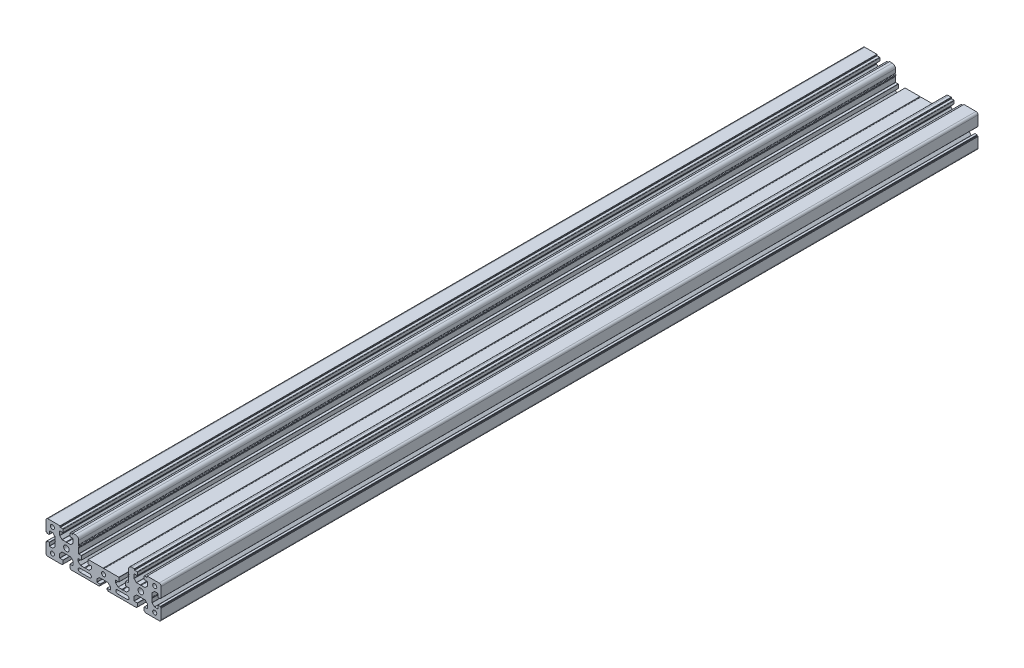
SolidWorks part; units mm, degrees
material "6063-T6"
ref_plane "Спереди" through (0, 0, 0) normal (0, 0, 1) x (1, 0, 0)
ref_plane "Сверху" through (0, 0, 0) normal (0, 1, 0) x (1, 0, 0)
ref_plane "Справа" through (0, 0, 0) normal (1, 0, 0) x (0, 0, -1)
sketch "Эскиз1" plane through (0, 0, 0) normal (0, 0, 1) x (1, 0, 0)
  line L2 (29, -16.95) -> (17, -16.95)
  line L3 (17, -12.75) -> (29, -12.75)
  line L4 (-29, -12.75) -> (-17, -12.75)
  line L5 (-17, -16.95) -> (-29, -16.95)
  line L6 (-53.1, 18.7) -> (-53.1, 19.8)
  line L7 (-53.3, 20) -> (-68, 20)
  line L8 (-70.5, 17.5) -> (-70.5, 5.4)
  line L9 (-70.3, 5.2) -> (-69.7, 5.2)
  line L10 (-69.5, 5) -> (-69.5, 4.3)
  line L11 (-69.3, 4.1) -> (-66.7, 4.1)
  line L12 (-66.5, 4.3) -> (-66.5, 8.05)
  line L13 (-66.3, 8.25) -> (-62.3828, 8.25)
  line L14 (-62.2414, 8.1914) -> (-59.3586, 5.3086)
  line L15 (-59.3, 5.1672) -> (-59.3, 0.6245)
  line L16 (-59.3, -0.6245) -> (-59.3, -5.1672)
  line L17 (-59.3586, -5.3086) -> (-62.2414, -8.1914)
  line L18 (-62.3828, -8.25) -> (-66.3, -8.25)
  line L19 (-66.5, -8.05) -> (-66.5, -4.3)
  line L20 (-66.7, -4.1) -> (-69.3, -4.1)
  line L21 (-69.5, -4.3) -> (-69.5, -5)
  line L22 (-69.7, -5.2) -> (-70.3, -5.2)
  line L23 (-70.5, -5.4) -> (-70.5, -17.5)
  line L24 (-68, -20) -> (-50.8, -20)
  line L25 (-50.6, -19.8) -> (-50.6, -19.2)
  line L26 (-50.4, -19) -> (-49.8, -19)
  line L27 (-49.6, -18.8) -> (-49.6, -14.7)
  line L28 (-49.8, -14.5) -> (-53.55, -14.5)
  line L29 (-53.75, -14.3) -> (-53.75, -9.7071)
  line L30 (-53.6036, -9.3536) -> (-50.8964, -6.6464)
  line L31 (-50.5429, -6.5) -> (-46.1245, -6.5)
  line L32 (-44.8755, -6.5) -> (-40.4571, -6.5)
  line L33 (-40.1036, -6.6464) -> (-37.3964, -9.3536)
  line L34 (-37.25, -9.7071) -> (-37.25, -14.3)
  line L35 (-37.45, -14.5) -> (-41.2, -14.5)
  line L36 (-41.4, -14.7) -> (-41.4, -18.8)
  line L37 (-41.2, -19) -> (-40.6, -19)
  line L38 (-40.4, -19.2) -> (-40.4, -19.8)
  line L39 (-40.2, -20) -> (-23.6245, -20)
  line L40 (-22.3755, -20) -> (-5.4, -20)
  line L41 (-5.2, -19.8) -> (-5.2, -19.2)
  line L42 (-5, -19) -> (-4.3, -19)
  line L43 (-4.1, -18.8) -> (-4.1, -17.5)
  line L44 (-4.3, -17.3) -> (-8.05, -17.3)
  line L45 (-8.25, -17.1) -> (-8.25, -13.8828)
  line L46 (-8.1914, -13.7414) -> (-5.3086, -10.8586)
  line L47 (-5.1672, -10.8) -> (-0.6245, -10.8)
  line L48 (0.6245, -10.8) -> (5.1672, -10.8)
  line L49 (5.3086, -10.8586) -> (8.1914, -13.7414)
  line L50 (8.25, -13.8828) -> (8.25, -17.1)
  line L51 (8.05, -17.3) -> (4.3, -17.3)
  line L52 (4.1, -17.5) -> (4.1, -18.8)
  line L53 (4.3, -19) -> (5, -19)
  line L54 (5.2, -19.2) -> (5.2, -19.8)
  line L55 (5.4, -20) -> (22.3755, -20)
  line L56 (23.6245, -20) -> (40.2, -20)
  line L57 (40.4, -19.8) -> (40.4, -19.2)
  line L58 (40.6, -19) -> (41.2, -19)
  line L59 (41.4, -18.8) -> (41.4, -14.7)
  line L60 (41.2, -14.5) -> (37.45, -14.5)
  line L61 (37.25, -14.3) -> (37.25, -9.7071)
  line L62 (37.3964, -9.3536) -> (40.1036, -6.6464)
  line L63 (40.4571, -6.5) -> (44.8755, -6.5)
  line L64 (46.1245, -6.5) -> (50.5429, -6.5)
  line L65 (50.8964, -6.6464) -> (53.6036, -9.3536)
  line L66 (53.75, -9.7071) -> (53.75, -14.3)
  line L67 (53.55, -14.5) -> (49.8, -14.5)
  line L68 (49.6, -14.7) -> (49.6, -18.8)
  line L69 (49.8, -19) -> (50.4, -19)
  line L70 (50.6, -19.2) -> (50.6, -19.8)
  line L71 (50.8, -20) -> (68, -20)
  line L72 (70.5, -17.5) -> (70.5, -5.4)
  line L73 (70.3, -5.2) -> (69.7, -5.2)
  line L74 (69.5, -5) -> (69.5, -4.3)
  line L75 (69.3, -4.1) -> (66.7, -4.1)
  line L76 (66.5, -4.3) -> (66.5, -8.05)
  line L77 (66.3, -8.25) -> (62.3828, -8.25)
  line L78 (62.2414, -8.1914) -> (59.3586, -5.3086)
  line L79 (59.3, -5.1672) -> (59.3, -0.6245)
  line L80 (59.3, 0.6245) -> (59.3, 5.1672)
  line L81 (59.3586, 5.3086) -> (62.2414, 8.1914)
  line L82 (62.3828, 8.25) -> (66.3, 8.25)
  line L83 (66.5, 8.05) -> (66.5, 4.3)
  line L84 (66.7, 4.1) -> (69.3, 4.1)
  line L85 (69.5, 4.3) -> (69.5, 5)
  line L86 (69.7, 5.2) -> (70.3, 5.2)
  line L87 (70.5, 5.4) -> (70.5, 17.5)
  line L88 (68, 20) -> (53.3, 20)
  line L89 (53.1, 19.8) -> (53.1, 18.7)
  line L90 (52.9, 18.5) -> (50.1, 18.5)
  line L91 (49.6, 18) -> (49.6, 14.7)
  line L92 (49.8, 14.5) -> (53.55, 14.5)
  line L93 (53.75, 14.3) -> (53.75, 9.7071)
  line L94 (53.6036, 9.3536) -> (50.8964, 6.6464)
  line L95 (50.5429, 6.5) -> (46.1245, 6.5)
  line L96 (44.8755, 6.5) -> (40.4571, 6.5)
  line L97 (40.1036, 6.6464) -> (37.3964, 9.3536)
  line L98 (37.25, 9.7071) -> (37.25, 14.3)
  line L99 (37.45, 14.5) -> (41.2, 14.5)
  line L100 (41.4, 14.7) -> (41.4, 18)
  line L101 (40.9, 18.5) -> (38.1, 18.5)
  line L102 (37.9, 18.7) -> (37.9, 19.8)
  line L103 (37.7, 20) -> (34.5, 20)
  line L104 (30.5, 16) -> (30.5, 11.366)
  line L105 (30.5, 7.634) -> (30.5, 1.7)
  line L106 (30.3, 1.5) -> (27.3, 1.5)
  line L107 (27.1, 1.3) -> (27.1, -3.3)
  line L108 (27.3, -3.5) -> (31.05, -3.5)
  line L109 (31.25, -3.7) -> (31.25, -6.4172)
  line L110 (31.1914, -6.5586) -> (28.3086, -9.4414)
  line L111 (28.1672, -9.5) -> (23.6245, -9.5)
  line L112 (22.3755, -9.5) -> (17.8328, -9.5)
  line L113 (17.6914, -9.4414) -> (14.8086, -6.5586)
  line L114 (14.75, -6.4172) -> (14.75, -3.7)
  line L115 (14.95, -3.5) -> (18.7, -3.5)
  line L116 (18.9, -3.3) -> (18.9, 1.3)
  line L117 (18.7, 1.5) -> (0.6245, 1.5)
  line L118 (-0.6245, 1.5) -> (-18.7, 1.5)
  line L119 (-18.9, 1.3) -> (-18.9, -3.3)
  line L120 (-18.7, -3.5) -> (-14.95, -3.5)
  line L121 (-14.75, -3.7) -> (-14.75, -6.4172)
  line L122 (-14.8086, -6.5586) -> (-17.6914, -9.4414)
  line L123 (-17.8328, -9.5) -> (-22.3755, -9.5)
  line L124 (-23.6245, -9.5) -> (-28.1672, -9.5)
  line L125 (-28.3086, -9.4414) -> (-31.1914, -6.5586)
  line L126 (-31.25, -6.4172) -> (-31.25, -3.7)
  line L127 (-31.05, -3.5) -> (-27.3, -3.5)
  line L128 (-27.1, -3.3) -> (-27.1, 1.3)
  line L129 (-27.3, 1.5) -> (-30.3, 1.5)
  line L130 (-30.5, 1.7) -> (-30.5, 7.634)
  line L131 (-30.5, 11.366) -> (-30.5, 16)
  line L132 (-34.5, 20) -> (-37.7, 20)
  line L133 (-37.9, 19.8) -> (-37.9, 18.7)
  line L134 (-38.1, 18.5) -> (-40.9, 18.5)
  line L135 (-41.4, 18) -> (-41.4, 14.7)
  line L136 (-41.2, 14.5) -> (-37.45, 14.5)
  line L137 (-37.25, 14.3) -> (-37.25, 9.7071)
  line L138 (-37.3964, 9.3536) -> (-40.1036, 6.6464)
  line L139 (-40.4571, 6.5) -> (-44.8755, 6.5)
  line L140 (-46.1245, 6.5) -> (-50.5429, 6.5)
  line L141 (-50.8964, 6.6464) -> (-53.6036, 9.3536)
  line L142 (-53.75, 9.7071) -> (-53.75, 14.3)
  line L143 (-53.55, 14.5) -> (-49.8, 14.5)
  line L144 (-49.6, 14.7) -> (-49.6, 18)
  line L145 (-50.1, 18.5) -> (-52.9, 18.5)
  arc A1 (17, -12.75) -> (17, -16.95) centre (17, -14.85) ccw
  arc A2 (29, -16.95) -> (29, -12.75) centre (29, -14.85) ccw
  circle A3 centre (62.625, 14.125) radius 2.5
  circle A4 centre (0, -4.65) radius 2.5
  circle A5 centre (-62.625, 14.125) radius 2.5
  circle A6 centre (-45.5, 0) radius 3.4
  circle A7 centre (-62.625, -14.125) radius 2.5
  circle A8 centre (45.5, 0) radius 3.4
  circle A9 centre (62.625, -14.125) radius 2.5
  arc A10 (-17, -16.95) -> (-17, -12.75) centre (-17, -14.85) ccw
  arc A11 (-29, -12.75) -> (-29, -16.95) centre (-29, -14.85) ccw
  arc A12 (-53.1, 18.7) -> (-52.9, 18.5) centre (-52.9, 18.7) ccw
  arc A13 (-53.1, 19.8) -> (-53.3, 20) centre (-53.3, 19.8) ccw
  arc A14 (-68, 20) -> (-70.5, 17.5) centre (-68, 17.5) ccw
  arc A15 (-70.5, 5.4) -> (-70.3, 5.2) centre (-70.3, 5.4) ccw
  arc A16 (-69.5, 5) -> (-69.7, 5.2) centre (-69.7, 5) ccw
  arc A17 (-69.5, 4.3) -> (-69.3, 4.1) centre (-69.3, 4.3) ccw
  arc A18 (-66.7, 4.1) -> (-66.5, 4.3) centre (-66.7, 4.3) ccw
  arc A19 (-66.3, 8.25) -> (-66.5, 8.05) centre (-66.3, 8.05) ccw
  arc A20 (-62.2414, 8.1914) -> (-62.3828, 8.25) centre (-62.3828, 8.05) ccw
  arc A21 (-59.3, 5.1672) -> (-59.3586, 5.3086) centre (-59.5, 5.1672) ccw
  arc A22 (-59.3, 0.6245) -> (-59.1875, 0.3903) centre (-59, 0.6245) ccw
  arc A23 (-59.1875, -0.3903) -> (-59.1875, 0.3903) centre (-59.5, 0) ccw
  arc A24 (-59.1875, -0.3903) -> (-59.3, -0.6245) centre (-59, -0.6245) ccw
  arc A25 (-59.3586, -5.3086) -> (-59.3, -5.1672) centre (-59.5, -5.1672) ccw
  arc A26 (-62.3828, -8.25) -> (-62.2414, -8.1914) centre (-62.3828, -8.05) ccw
  arc A27 (-66.5, -8.05) -> (-66.3, -8.25) centre (-66.3, -8.05) ccw
  arc A28 (-66.5, -4.3) -> (-66.7, -4.1) centre (-66.7, -4.3) ccw
  arc A29 (-69.3, -4.1) -> (-69.5, -4.3) centre (-69.3, -4.3) ccw
  arc A30 (-69.7, -5.2) -> (-69.5, -5) centre (-69.7, -5) ccw
  arc A31 (-70.3, -5.2) -> (-70.5, -5.4) centre (-70.3, -5.4) ccw
  arc A32 (-70.5, -17.5) -> (-68, -20) centre (-68, -17.5) ccw
  arc A33 (-50.8, -20) -> (-50.6, -19.8) centre (-50.8, -19.8) ccw
  arc A34 (-50.4, -19) -> (-50.6, -19.2) centre (-50.4, -19.2) ccw
  arc A35 (-49.8, -19) -> (-49.6, -18.8) centre (-49.8, -18.8) ccw
  arc A36 (-49.6, -14.7) -> (-49.8, -14.5) centre (-49.8, -14.7) ccw
  arc A37 (-53.75, -14.3) -> (-53.55, -14.5) centre (-53.55, -14.3) ccw
  arc A38 (-53.6036, -9.3536) -> (-53.75, -9.7071) centre (-53.25, -9.7071) ccw
  arc A39 (-50.5429, -6.5) -> (-50.8964, -6.6464) centre (-50.5429, -7) ccw
  arc A40 (-46.1245, -6.5) -> (-45.8903, -6.3875) centre (-46.1245, -6.2) ccw
  arc A41 (-45.1097, -6.3875) -> (-45.8903, -6.3875) centre (-45.5, -6.7) ccw
  arc A42 (-45.1097, -6.3875) -> (-44.8755, -6.5) centre (-44.8755, -6.2) ccw
  arc A43 (-40.1036, -6.6464) -> (-40.4571, -6.5) centre (-40.4571, -7) ccw
  arc A44 (-37.25, -9.7071) -> (-37.3964, -9.3536) centre (-37.75, -9.7071) ccw
  arc A45 (-37.45, -14.5) -> (-37.25, -14.3) centre (-37.45, -14.3) ccw
  arc A46 (-41.2, -14.5) -> (-41.4, -14.7) centre (-41.2, -14.7) ccw
  arc A47 (-41.4, -18.8) -> (-41.2, -19) centre (-41.2, -18.8) ccw
  arc A48 (-40.4, -19.2) -> (-40.6, -19) centre (-40.6, -19.2) ccw
  arc A49 (-40.4, -19.8) -> (-40.2, -20) centre (-40.2, -19.8) ccw
  arc A50 (-23.6245, -20) -> (-23.3903, -19.8875) centre (-23.6245, -19.7) ccw
  arc A51 (-22.6097, -19.8875) -> (-23.3903, -19.8875) centre (-23, -20.2) ccw
  arc A52 (-22.6097, -19.8875) -> (-22.3755, -20) centre (-22.3755, -19.7) ccw
  arc A53 (-5.4, -20) -> (-5.2, -19.8) centre (-5.4, -19.8) ccw
  arc A54 (-5, -19) -> (-5.2, -19.2) centre (-5, -19.2) ccw
  arc A55 (-4.3, -19) -> (-4.1, -18.8) centre (-4.3, -18.8) ccw
  arc A56 (-4.1, -17.5) -> (-4.3, -17.3) centre (-4.3, -17.5) ccw
  arc A57 (-8.25, -17.1) -> (-8.05, -17.3) centre (-8.05, -17.1) ccw
  arc A58 (-8.1914, -13.7414) -> (-8.25, -13.8828) centre (-8.05, -13.8828) ccw
  arc A59 (-5.1672, -10.8) -> (-5.3086, -10.8586) centre (-5.1672, -11) ccw
  arc A60 (-0.6245, -10.8) -> (-0.3903, -10.6875) centre (-0.6245, -10.5) ccw
  arc A61 (0.3903, -10.6875) -> (-0.3903, -10.6875) centre (0, -11) ccw
  arc A62 (0.3903, -10.6875) -> (0.6245, -10.8) centre (0.6245, -10.5) ccw
  arc A63 (5.3086, -10.8586) -> (5.1672, -10.8) centre (5.1672, -11) ccw
  arc A64 (8.25, -13.8828) -> (8.1914, -13.7414) centre (8.05, -13.8828) ccw
  arc A65 (8.05, -17.3) -> (8.25, -17.1) centre (8.05, -17.1) ccw
  arc A66 (4.3, -17.3) -> (4.1, -17.5) centre (4.3, -17.5) ccw
  arc A67 (4.1, -18.8) -> (4.3, -19) centre (4.3, -18.8) ccw
  arc A68 (5.2, -19.2) -> (5, -19) centre (5, -19.2) ccw
  arc A69 (5.2, -19.8) -> (5.4, -20) centre (5.4, -19.8) ccw
  arc A70 (22.3755, -20) -> (22.6097, -19.8875) centre (22.3755, -19.7) ccw
  arc A71 (23.3903, -19.8875) -> (22.6097, -19.8875) centre (23, -20.2) ccw
  arc A72 (23.3903, -19.8875) -> (23.6245, -20) centre (23.6245, -19.7) ccw
  arc A73 (40.2, -20) -> (40.4, -19.8) centre (40.2, -19.8) ccw
  arc A74 (40.6, -19) -> (40.4, -19.2) centre (40.6, -19.2) ccw
  arc A75 (41.2, -19) -> (41.4, -18.8) centre (41.2, -18.8) ccw
  arc A76 (41.4, -14.7) -> (41.2, -14.5) centre (41.2, -14.7) ccw
  arc A77 (37.25, -14.3) -> (37.45, -14.5) centre (37.45, -14.3) ccw
  arc A78 (37.3964, -9.3536) -> (37.25, -9.7071) centre (37.75, -9.7071) ccw
  arc A79 (40.4571, -6.5) -> (40.1036, -6.6464) centre (40.4571, -7) ccw
  arc A80 (44.8755, -6.5) -> (45.1097, -6.3875) centre (44.8755, -6.2) ccw
  arc A81 (45.8903, -6.3875) -> (45.1097, -6.3875) centre (45.5, -6.7) ccw
  arc A82 (45.8903, -6.3875) -> (46.1245, -6.5) centre (46.1245, -6.2) ccw
  arc A83 (50.8964, -6.6464) -> (50.5429, -6.5) centre (50.5429, -7) ccw
  arc A84 (53.75, -9.7071) -> (53.6036, -9.3536) centre (53.25, -9.7071) ccw
  arc A85 (53.55, -14.5) -> (53.75, -14.3) centre (53.55, -14.3) ccw
  arc A86 (49.8, -14.5) -> (49.6, -14.7) centre (49.8, -14.7) ccw
  arc A87 (49.6, -18.8) -> (49.8, -19) centre (49.8, -18.8) ccw
  arc A88 (50.6, -19.2) -> (50.4, -19) centre (50.4, -19.2) ccw
  arc A89 (50.6, -19.8) -> (50.8, -20) centre (50.8, -19.8) ccw
  arc A90 (68, -20) -> (70.5, -17.5) centre (68, -17.5) ccw
  arc A91 (70.5, -5.4) -> (70.3, -5.2) centre (70.3, -5.4) ccw
  arc A92 (69.5, -5) -> (69.7, -5.2) centre (69.7, -5) ccw
  arc A93 (69.5, -4.3) -> (69.3, -4.1) centre (69.3, -4.3) ccw
  arc A94 (66.7, -4.1) -> (66.5, -4.3) centre (66.7, -4.3) ccw
  arc A95 (66.3, -8.25) -> (66.5, -8.05) centre (66.3, -8.05) ccw
  arc A96 (62.2414, -8.1914) -> (62.3828, -8.25) centre (62.3828, -8.05) ccw
  arc A97 (59.3, -5.1672) -> (59.3586, -5.3086) centre (59.5, -5.1672) ccw
  arc A98 (59.3, -0.6245) -> (59.1875, -0.3903) centre (59, -0.6245) ccw
  arc A99 (59.1875, 0.3903) -> (59.1875, -0.3903) centre (59.5, 0) ccw
  arc A100 (59.1875, 0.3903) -> (59.3, 0.6245) centre (59, 0.6245) ccw
  arc A101 (59.3586, 5.3086) -> (59.3, 5.1672) centre (59.5, 5.1672) ccw
  arc A102 (62.3828, 8.25) -> (62.2414, 8.1914) centre (62.3828, 8.05) ccw
  arc A103 (66.5, 8.05) -> (66.3, 8.25) centre (66.3, 8.05) ccw
  arc A104 (66.5, 4.3) -> (66.7, 4.1) centre (66.7, 4.3) ccw
  arc A105 (69.3, 4.1) -> (69.5, 4.3) centre (69.3, 4.3) ccw
  arc A106 (69.7, 5.2) -> (69.5, 5) centre (69.7, 5) ccw
  arc A107 (70.3, 5.2) -> (70.5, 5.4) centre (70.3, 5.4) ccw
  arc A108 (70.5, 17.5) -> (68, 20) centre (68, 17.5) ccw
  arc A109 (53.3, 20) -> (53.1, 19.8) centre (53.3, 19.8) ccw
  arc A110 (52.9, 18.5) -> (53.1, 18.7) centre (52.9, 18.7) ccw
  arc A111 (50.1, 18.5) -> (49.6, 18) centre (50.1, 18) ccw
  arc A112 (49.6, 14.7) -> (49.8, 14.5) centre (49.8, 14.7) ccw
  arc A113 (53.75, 14.3) -> (53.55, 14.5) centre (53.55, 14.3) ccw
  arc A114 (53.6036, 9.3536) -> (53.75, 9.7071) centre (53.25, 9.7071) ccw
  arc A115 (50.5429, 6.5) -> (50.8964, 6.6464) centre (50.5429, 7) ccw
  arc A116 (46.1245, 6.5) -> (45.8903, 6.3875) centre (46.1245, 6.2) ccw
  arc A117 (45.1097, 6.3875) -> (45.8903, 6.3875) centre (45.5, 6.7) ccw
  arc A118 (45.1097, 6.3875) -> (44.8755, 6.5) centre (44.8755, 6.2) ccw
  arc A119 (40.1036, 6.6464) -> (40.4571, 6.5) centre (40.4571, 7) ccw
  arc A120 (37.25, 9.7071) -> (37.3964, 9.3536) centre (37.75, 9.7071) ccw
  arc A121 (37.45, 14.5) -> (37.25, 14.3) centre (37.45, 14.3) ccw
  arc A122 (41.2, 14.5) -> (41.4, 14.7) centre (41.2, 14.7) ccw
  arc A123 (41.4, 18) -> (40.9, 18.5) centre (40.9, 18) ccw
  arc A124 (37.9, 18.7) -> (38.1, 18.5) centre (38.1, 18.7) ccw
  arc A125 (37.9, 19.8) -> (37.7, 20) centre (37.7, 19.8) ccw
  arc A126 (34.5, 20) -> (30.5, 16) centre (34.5, 16) ccw
  arc A127 (30.5, 11.366) -> (30.75, 10.933) centre (31, 11.366) ccw
  arc A128 (30.5, 10) -> (30.75, 10.933) centre (30.5, 10.5) ccw
  arc A129 (30.5, 10) -> (30.5, 9) centre (30.5, 9.5) ccw
  arc A130 (30.75, 8.067) -> (30.5, 9) centre (30.5, 8.5) ccw
  arc A131 (30.75, 8.067) -> (30.5, 7.634) centre (31, 7.634) ccw
  arc A132 (30.3, 1.5) -> (30.5, 1.7) centre (30.3, 1.7) ccw
  arc A133 (27.3, 1.5) -> (27.1, 1.3) centre (27.3, 1.3) ccw
  arc A134 (27.1, -3.3) -> (27.3, -3.5) centre (27.3, -3.3) ccw
  arc A135 (31.25, -3.7) -> (31.05, -3.5) centre (31.05, -3.7) ccw
  arc A136 (31.1914, -6.5586) -> (31.25, -6.4172) centre (31.05, -6.4172) ccw
  arc A137 (28.1672, -9.5) -> (28.3086, -9.4414) centre (28.1672, -9.3) ccw
  arc A138 (23.6245, -9.5) -> (23.3903, -9.6125) centre (23.6245, -9.8) ccw
  arc A139 (22.6097, -9.6125) -> (23.3903, -9.6125) centre (23, -9.3) ccw
  arc A140 (22.6097, -9.6125) -> (22.3755, -9.5) centre (22.3755, -9.8) ccw
  arc A141 (17.6914, -9.4414) -> (17.8328, -9.5) centre (17.8328, -9.3) ccw
  arc A142 (14.75, -6.4172) -> (14.8086, -6.5586) centre (14.95, -6.4172) ccw
  arc A143 (14.95, -3.5) -> (14.75, -3.7) centre (14.95, -3.7) ccw
  arc A144 (18.7, -3.5) -> (18.9, -3.3) centre (18.7, -3.3) ccw
  arc A145 (18.9, 1.3) -> (18.7, 1.5) centre (18.7, 1.3) ccw
  arc A146 (0.6245, 1.5) -> (0.3903, 1.3875) centre (0.6245, 1.2) ccw
  arc A147 (-0.3903, 1.3875) -> (0.3903, 1.3875) centre (0, 1.7) ccw
  arc A148 (-0.3903, 1.3875) -> (-0.6245, 1.5) centre (-0.6245, 1.2) ccw
  arc A149 (-18.7, 1.5) -> (-18.9, 1.3) centre (-18.7, 1.3) ccw
  arc A150 (-18.9, -3.3) -> (-18.7, -3.5) centre (-18.7, -3.3) ccw
  arc A151 (-14.75, -3.7) -> (-14.95, -3.5) centre (-14.95, -3.7) ccw
  arc A152 (-14.8086, -6.5586) -> (-14.75, -6.4172) centre (-14.95, -6.4172) ccw
  arc A153 (-17.8328, -9.5) -> (-17.6914, -9.4414) centre (-17.8328, -9.3) ccw
  arc A154 (-22.3755, -9.5) -> (-22.6097, -9.6125) centre (-22.3755, -9.8) ccw
  arc A155 (-23.3903, -9.6125) -> (-22.6097, -9.6125) centre (-23, -9.3) ccw
  arc A156 (-23.3903, -9.6125) -> (-23.6245, -9.5) centre (-23.6245, -9.8) ccw
  arc A157 (-28.3086, -9.4414) -> (-28.1672, -9.5) centre (-28.1672, -9.3) ccw
  arc A158 (-31.25, -6.4172) -> (-31.1914, -6.5586) centre (-31.05, -6.4172) ccw
  arc A159 (-31.05, -3.5) -> (-31.25, -3.7) centre (-31.05, -3.7) ccw
  arc A160 (-27.3, -3.5) -> (-27.1, -3.3) centre (-27.3, -3.3) ccw
  arc A161 (-27.1, 1.3) -> (-27.3, 1.5) centre (-27.3, 1.3) ccw
  arc A162 (-30.5, 1.7) -> (-30.3, 1.5) centre (-30.3, 1.7) ccw
  arc A163 (-30.5, 7.634) -> (-30.75, 8.067) centre (-31, 7.634) ccw
  arc A164 (-30.5, 9) -> (-30.75, 8.067) centre (-30.5, 8.5) ccw
  arc A165 (-30.5, 9) -> (-30.5, 10) centre (-30.5, 9.5) ccw
  arc A166 (-30.75, 10.933) -> (-30.5, 10) centre (-30.5, 10.5) ccw
  arc A167 (-30.75, 10.933) -> (-30.5, 11.366) centre (-31, 11.366) ccw
  arc A168 (-30.5, 16) -> (-34.5, 20) centre (-34.5, 16) ccw
  arc A169 (-37.7, 20) -> (-37.9, 19.8) centre (-37.7, 19.8) ccw
  arc A170 (-38.1, 18.5) -> (-37.9, 18.7) centre (-38.1, 18.7) ccw
  arc A171 (-40.9, 18.5) -> (-41.4, 18) centre (-40.9, 18) ccw
  arc A172 (-41.4, 14.7) -> (-41.2, 14.5) centre (-41.2, 14.7) ccw
  arc A173 (-37.25, 14.3) -> (-37.45, 14.5) centre (-37.45, 14.3) ccw
  arc A174 (-37.3964, 9.3536) -> (-37.25, 9.7071) centre (-37.75, 9.7071) ccw
  arc A175 (-40.4571, 6.5) -> (-40.1036, 6.6464) centre (-40.4571, 7) ccw
  arc A176 (-44.8755, 6.5) -> (-45.1097, 6.3875) centre (-44.8755, 6.2) ccw
  arc A177 (-45.8903, 6.3875) -> (-45.1097, 6.3875) centre (-45.5, 6.7) ccw
  arc A178 (-45.8903, 6.3875) -> (-46.1245, 6.5) centre (-46.1245, 6.2) ccw
  arc A179 (-50.8964, 6.6464) -> (-50.5429, 6.5) centre (-50.5429, 7) ccw
  arc A180 (-53.75, 9.7071) -> (-53.6036, 9.3536) centre (-53.25, 9.7071) ccw
  arc A181 (-53.55, 14.5) -> (-53.75, 14.3) centre (-53.55, 14.3) ccw
  arc A182 (-49.8, 14.5) -> (-49.6, 14.7) centre (-49.8, 14.7) ccw
  arc A183 (-49.6, 18) -> (-50.1, 18.5) centre (-50.1, 18) ccw
extrude "Бобышка-Вытянуть1" add sketch "Эскиз1" against normal blind 1000
